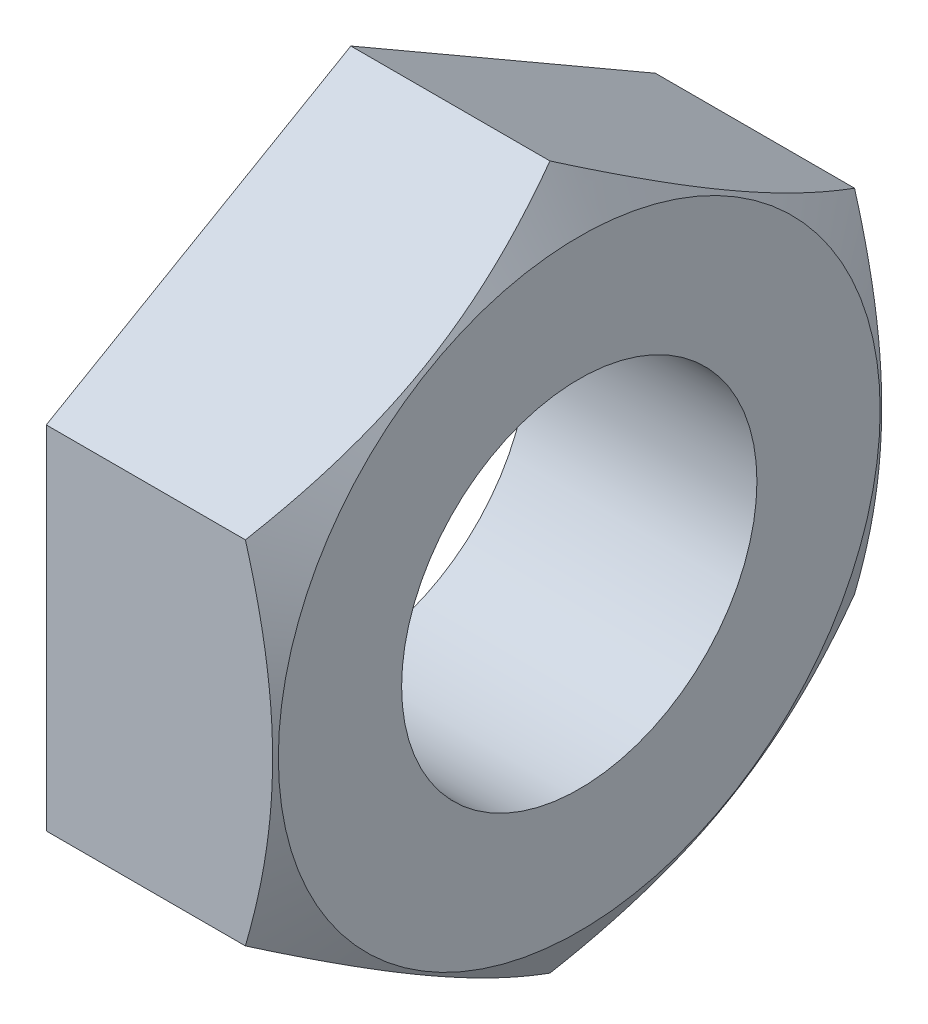
SolidWorks part; units mm, degrees
material "Stainless Steel (ferritic)"
ref_plane "Front" through (0, 0, 0) normal (0, 0, 1) x (1, 0, 0)
ref_plane "Top" through (0, 0, 0) normal (0, 1, 0) x (1, 0, 0)
ref_plane "Right" through (0, 0, 0) normal (1, 0, 0) x (0, 0, -1)
sketch "Sketch1" plane through (0, 0, 0) normal (1, 0, 0) x (0, 0, -1)
  line L0 (0, 24.5519) -> (0, -24.7706) construction
  line L1 (-33.1369, 0) -> (36.8552, 0) construction
  line L3 (12, 6.9282) -> (0, 13.8564)
  line L4 (0, 13.8564) -> (-12, 6.9282)
  line L5 (-12, 6.9282) -> (-12, -6.9282)
  line L6 (-12, -6.9282) -> (0, -13.8564)
  line L7 (0, -13.8564) -> (12, -6.9282)
  line L8 (12, -6.9282) -> (12, 6.9282)
  circle A0 centre (0, 0) radius 12 construction
  dimension "D1" = 24
extrude "Boss-Extrude1" add sketch "Sketch1" against normal blind 9
hole_wizard "M16x2.0 Tapped Hole1" positions "Sketch2" profile "Sketch3" tap size "M16x2.0" standard "ANSI Metric" end condition up to next
sketch "Sketch2" plane through (0, 0, 0) normal (1, 0, 0) x (0, 0, -1)
  point P0 (0, 0)
sketch "Sketch3" plane through (0, 0, 0) normal (0, 1, 0) x (0, 0, -1)
  line L0 (0, 0) -> (0, 9)
  line L1 (0, 9) -> (7, 9)
  line L2 (7, 9) -> (7, 0)
  line L5 (7, 0) -> (0, 0)
  line L11 (0, -6.35) -> (0, 107.95) construction
  dimension "Thru Tap Drill Dia." = 14
  dimension "Thru Tap Drill Depth" = 9
cosmetic thread "Hole Thread1" parameters "D2"=16
sketch "Sketch10" plane through (0, 0, 0) normal (0, 0, 1) x (1, 0, 0)
  line L0 (0, 13.8564) -> (0, 11.8564)
  line L1 (0, 11.8564) -> (-1.1547, 13.8564)
  line L2 (-9, 13.8564) -> (0, 13.8564) construction
  line L3 (-1.1547, 13.8564) -> (0, 13.8564)
  line L4 (-1.1547, 13.8564) -> (8.7715, -3.3363) construction
  dimension "D1" = 2
  dimension "D2" = 30
revolve "Cut-Revolve1" cut sketch "Sketch10" angle 360 about axis through (0, 0, 0) along (1, 0, 0)
